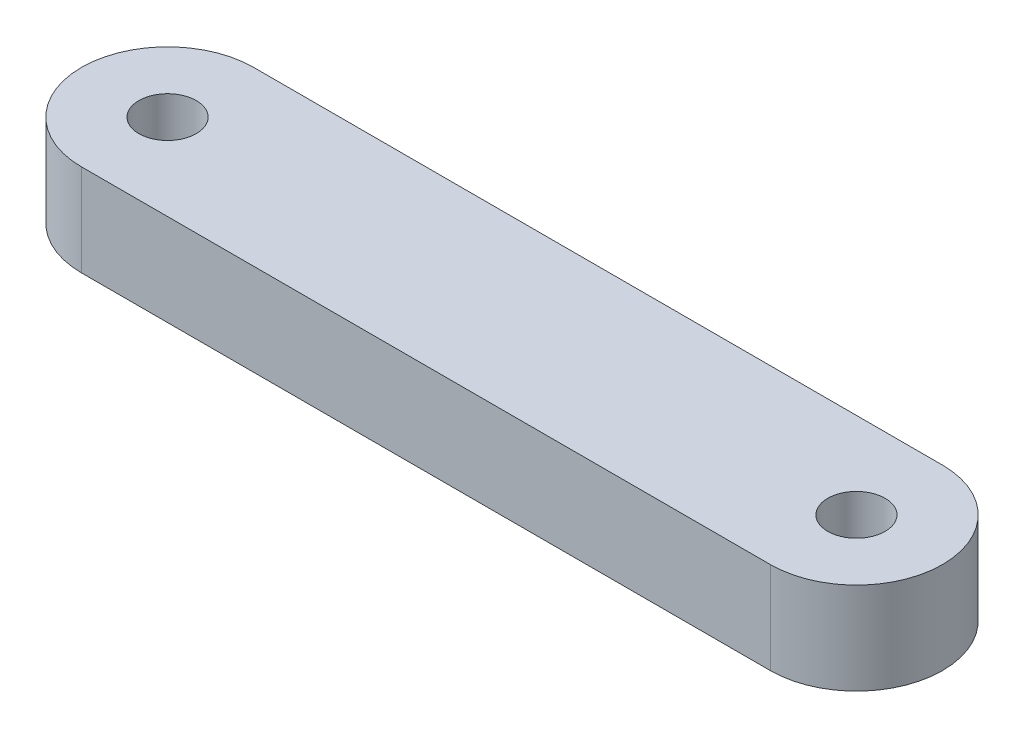
SolidWorks part; units mm, degrees
ref_plane "Front Plane" through (0, 0, 0) normal (0, 0, 1) x (1, 0, 0)
ref_plane "Top Plane" through (0, 0, 0) normal (0, 1, 0) x (1, 0, 0)
ref_plane "Right Plane" through (0, 0, 0) normal (1, 0, 0) x (0, 0, -1)
sketch "Sketch1" plane through (0, 0, 0) normal (0, 1, 0) x (1, 0, 0)
  line L0 (0, 37.5) -> (300, 37.5)
  line L1 (0, -37.5) -> (300, -37.5)
  circle A0 centre (0, 0) radius 12.5
  circle A1 centre (300, 0) radius 12.5
  arc A2 (0, 37.5) -> (0, -37.5) centre (0, 0) ccw
  arc A3 (300, -37.5) -> (300, 37.5) centre (300, 0) ccw
  dimension "D1" = 25
  dimension "D2" = 25
  dimension "D4" = 75
  dimension "D5" = 75
  dimension "D3" = 300
extrude "Boss-Extrude1" add sketch "Sketch1" along normal blind 40
